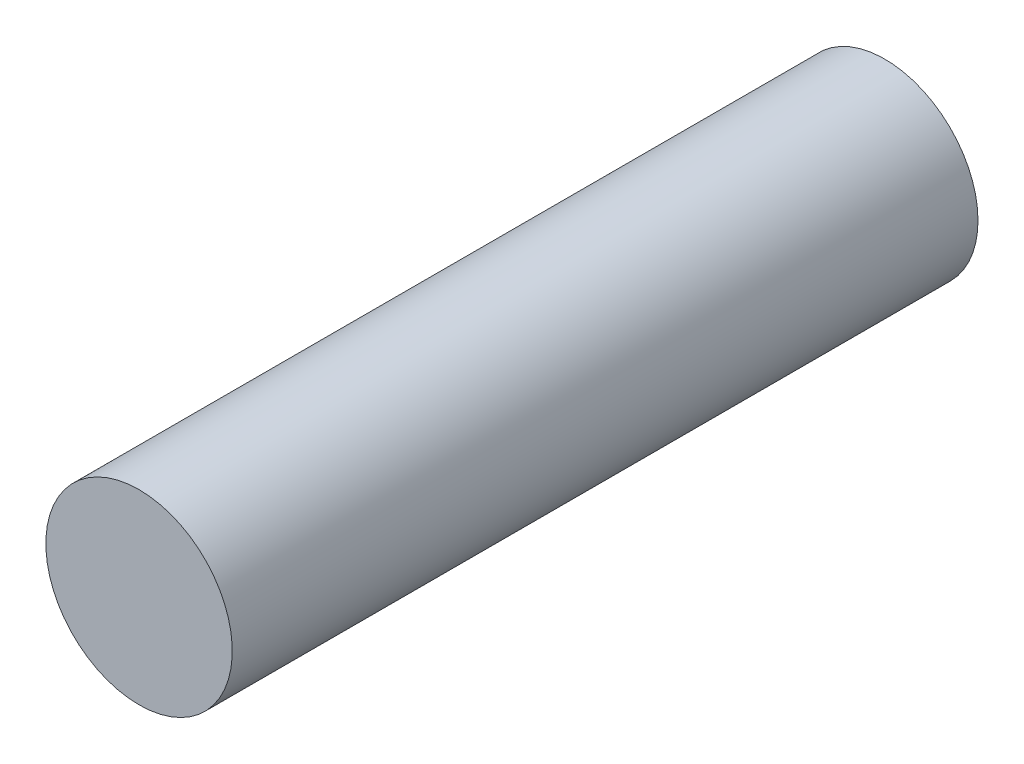
SolidWorks part; units mm, degrees
ref_plane "Front Plane" through (0, 0, 0) normal (0, 0, 1) x (1, 0, 0)
ref_plane "Top Plane" through (0, 0, 0) normal (0, 1, 0) x (1, 0, 0)
ref_plane "Right Plane" through (0, 0, 0) normal (1, 0, 0) x (0, 0, -1)
sketch "Sketch1" plane through (0, 0, 0) normal (0, 0, 1) x (1, 0, 0)
  circle A0 centre (0, 0) radius 1
extrude "Boss-Extrude1" add sketch "Sketch1" along normal up to surface (8 mm away) from surface
